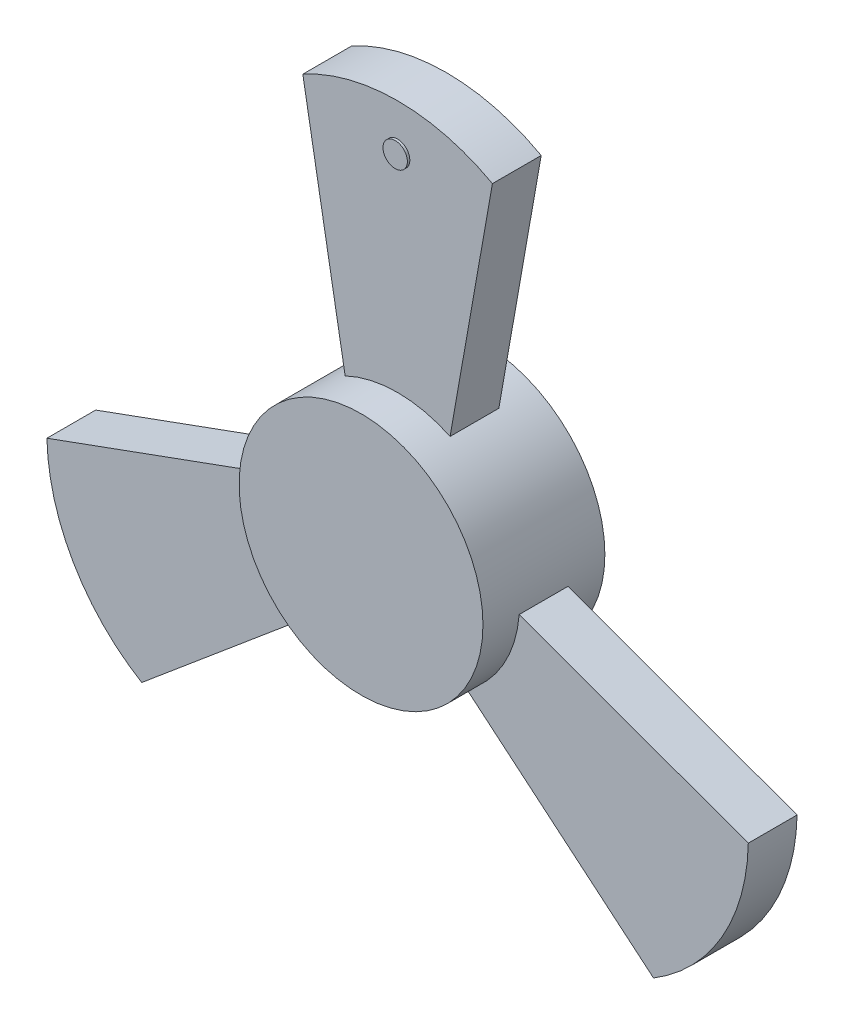
SolidWorks part; units mm, degrees
ref_plane "Front Plane" through (0, 0, 0) normal (0, 0, 1) x (1, 0, 0)
ref_plane "Top Plane" through (0, 0, 0) normal (0, 1, 0) x (1, 0, 0)
ref_plane "Right Plane" through (0, 0, 0) normal (1, 0, 0) x (0, 0, -1)
sketch "Sketch1" plane through (0, 0, 0) normal (0, 0, 1) x (1, 0, 0)
  circle A0 centre (0, 0) radius 50
  dimension "D1" = 100
extrude "Boss-Extrude1" add sketch "Sketch1" along normal mid plane 50
sketch "Sketch2" plane through (0, 0, 0) normal (0, 0, 1) x (1, 0, 0)
  line L0 (0, 0) -> (0, 153.9372) construction
  line L1 (-21.5108, 45.1363) -> (-38.8756, 143.6171)
  line L3 (38.8756, 143.6171) -> (21.5108, 45.1363)
  line L4 (104.9382, -105.4758) -> (28.3338, -41.1971)
  line L5 (49.8446, -3.9392) -> (143.8138, -38.1412)
  line L6 (-143.8138, -38.1412) -> (-49.8446, -3.9392)
  line L7 (-28.3338, -41.1971) -> (-104.9382, -105.4758)
  arc A0 (-21.5108, 45.1363) -> (21.5108, 45.1363) centre (0, 0) cw
  circle A1 centre (0, 0) radius 50 construction
  arc A2 (-38.8756, 143.6171) -> (38.8756, 143.6171) centre (0, 73.0513) cw
  arc A3 (143.8138, -38.1412) -> (104.9382, -105.4758) centre (63.2643, -36.5256) cw
  arc A4 (49.8446, -3.9392) -> (28.3338, -41.1971) centre (0, 0) cw
  arc A5 (-104.9382, -105.4758) -> (-143.8138, -38.1412) centre (-63.2643, -36.5256) cw
  arc A6 (-28.3338, -41.1971) -> (-49.8446, -3.9392) centre (0, 0) cw
  point P10 (0, 153.6171)
  point P24 (0, 0)
  dimension "D1" = 20
  dimension "D2" = 100
  dimension "D3" = 100
  dimension "D4" = 10
  dimension "D5" = 3
extrude "Boss-Extrude2" add sketch "Sketch2" along normal mid plane 20
sketch "Sketch3" plane through (0, 0, 10) normal (0, 0, 1) x (1, 0, 0)
  line L0 (0, 0) -> (0, 164.8058) construction
  circle A0 centre (0, 135) radius 5
  dimension "D1" = 10
  dimension "D2" = 135
extrude "Boss-Extrude3" add sketch "Sketch3" along normal mid plane 2
